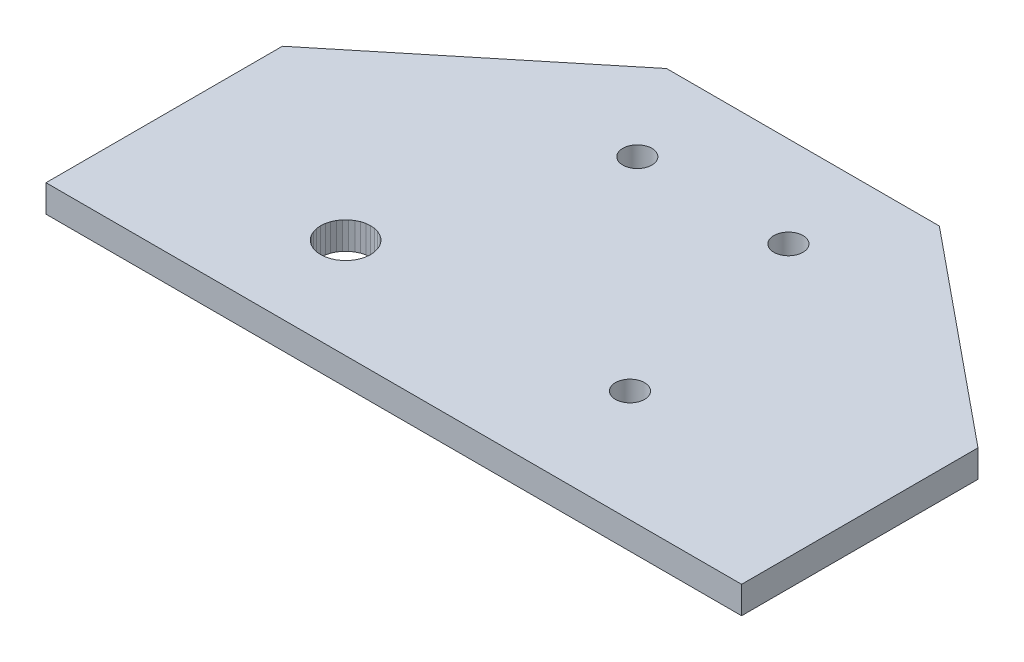
SolidWorks part; units mm, degrees
ref_plane "Front Plane" through (0, 0, 0) normal (0, 0, 1) x (1, 0, 0)
ref_plane "Top Plane" through (0, 0, 0) normal (0, 1, 0) x (1, 0, 0)
ref_plane "Right Plane" through (0, 0, 0) normal (1, 0, 0) x (0, 0, -1)
ref_plane "Plane1" through (0, 13, 0) normal (0, 1, 0) x (1, 0, 0)
sketch "Sketch1" plane through (0, 13, 0) normal (0, 1, 0) x (1, 0, 0)
  line L0 (0, -45) -> (76.5, -45)
  line L1 (76.5, -45) -> (76.5, -19)
  line L2 (76.5, -19) -> (53.25, 0)
  line L3 (53.25, 0) -> (23.25, 0)
  line L4 (23.25, 0) -> (0, -19)
  line L5 (0, -19) -> (0, -45)
extrude "Boss-Extrude1" add sketch "Sketch1" against normal blind 3
sketch "Sketch2" plane through (0, 10, 0) normal (0, -1, 0) x (1, 0, 0)
  line L0 (24.3316, 35.375) -> (24.0566, 35.7677)
  line L1 (24.0566, 35.7677) -> (23.7177, 36.1066)
  line L2 (23.7177, 36.1066) -> (23.325, 36.3816)
  line L3 (23.325, 36.3816) -> (22.8906, 36.5842)
  line L4 (22.8906, 36.5842) -> (22.4275, 36.7082)
  line L5 (22.4275, 36.7082) -> (21.95, 36.75)
  line L6 (21.95, 36.75) -> (21.4725, 36.7082)
  line L7 (21.4725, 36.7082) -> (21.0094, 36.5842)
  line L8 (21.0094, 36.5842) -> (20.575, 36.3816)
  line L9 (20.575, 36.3816) -> (20.1823, 36.1066)
  line L10 (20.1823, 36.1066) -> (19.8434, 35.7677)
  line L11 (19.8434, 35.7677) -> (19.5684, 35.375)
  line L12 (19.5684, 35.375) -> (19.3658, 34.9406)
  line L13 (19.3658, 34.9406) -> (19.2418, 34.4775)
  line L14 (19.2418, 34.4775) -> (19.2, 34)
  line L15 (19.2, 34) -> (19.2418, 33.5225)
  line L16 (19.2418, 33.5225) -> (19.3658, 33.0594)
  line L17 (19.3658, 33.0594) -> (19.5684, 32.625)
  line L18 (19.5684, 32.625) -> (19.8434, 32.2323)
  line L19 (19.8434, 32.2323) -> (20.1823, 31.8934)
  line L20 (20.1823, 31.8934) -> (20.575, 31.6184)
  line L21 (20.575, 31.6184) -> (21.0094, 31.4158)
  line L22 (21.0094, 31.4158) -> (21.4725, 31.2918)
  line L23 (21.4725, 31.2918) -> (21.95, 31.25)
  line L24 (21.95, 31.25) -> (22.4275, 31.2918)
  line L25 (22.4275, 31.2918) -> (22.8906, 31.4158)
  line L26 (22.8906, 31.4158) -> (23.325, 31.6184)
  line L27 (23.325, 31.6184) -> (23.7177, 31.8934)
  line L28 (23.7177, 31.8934) -> (24.0566, 32.2323)
  line L29 (24.0566, 32.2323) -> (24.3316, 32.625)
  line L30 (24.3316, 32.625) -> (24.5342, 33.0594)
  line L31 (24.5342, 33.0594) -> (24.6582, 33.5225)
  line L32 (24.6582, 33.5225) -> (24.7, 34)
  line L33 (24.7, 34) -> (24.6582, 34.4775)
  line L34 (24.6582, 34.4775) -> (24.5342, 34.9406)
  line L35 (24.5342, 34.9406) -> (24.3316, 35.375)
extrude "Cut-Extrude1" cut sketch "Sketch2" against normal through all
sketch "Sketch3" plane through (0, 13, 0) normal (0, 1, 0) x (-1, 0, 0)
  line L0 (-52.7747, 30.3008) -> (-53.1696, 30.4849)
  line L1 (-53.1696, 30.4849) -> (-53.5266, 30.7349)
  line L2 (-53.5266, 30.7349) -> (-53.8347, 31.043)
  line L3 (-53.8347, 31.043) -> (-54.0847, 31.4)
  line L4 (-54.0847, 31.4) -> (-54.2688, 31.795)
  line L5 (-54.2688, 31.795) -> (-54.3816, 32.2159)
  line L6 (-54.3816, 32.2159) -> (-54.4196, 32.65)
  line L7 (-54.4196, 32.65) -> (-54.3816, 33.0841)
  line L8 (-54.3816, 33.0841) -> (-54.2688, 33.5051)
  line L9 (-54.2688, 33.5051) -> (-54.0847, 33.9)
  line L10 (-54.0847, 33.9) -> (-53.8347, 34.257)
  line L11 (-53.8347, 34.257) -> (-53.5266, 34.5651)
  line L12 (-53.5266, 34.5651) -> (-53.1696, 34.8151)
  line L13 (-53.1696, 34.8151) -> (-52.7747, 34.9992)
  line L14 (-52.7747, 34.9992) -> (-52.3537, 35.112)
  line L15 (-52.3537, 35.112) -> (-51.9196, 35.15)
  line L16 (-51.9196, 35.15) -> (-51.4855, 35.112)
  line L17 (-51.4855, 35.112) -> (-51.0646, 34.9992)
  line L18 (-51.0646, 34.9992) -> (-50.6696, 34.8151)
  line L19 (-50.6696, 34.8151) -> (-50.3126, 34.5651)
  line L20 (-50.3126, 34.5651) -> (-50.0045, 34.257)
  line L21 (-50.0045, 34.257) -> (-49.7545, 33.9)
  line L22 (-49.7545, 33.9) -> (-49.5704, 33.5051)
  line L23 (-49.5704, 33.5051) -> (-49.4576, 33.0841)
  line L24 (-49.4576, 33.0841) -> (-49.4196, 32.65)
  line L25 (-49.4196, 32.65) -> (-49.4576, 32.2159)
  line L26 (-49.4576, 32.2159) -> (-49.5704, 31.795)
  line L27 (-49.5704, 31.795) -> (-49.7545, 31.4)
  line L28 (-49.7545, 31.4) -> (-50.0045, 31.043)
  line L29 (-50.0045, 31.043) -> (-50.3126, 30.7349)
  line L30 (-50.3126, 30.7349) -> (-50.6696, 30.4849)
  line L31 (-50.6696, 30.4849) -> (-51.0646, 30.3008)
  line L32 (-51.0646, 30.3008) -> (-51.4855, 30.188)
  line L33 (-51.4855, 30.188) -> (-51.9196, 30.15)
  line L34 (-51.9196, 30.15) -> (-52.3537, 30.188)
  line L35 (-52.3537, 30.188) -> (-52.7747, 30.3008)
sketch "Sketch4" plane through (0, 13, 0) normal (0, 1, 0) x (-1, 0, 0)
  line L0 (-41.95, 10.3473) -> (-41.9196, 10)
  line L1 (-41.9196, 10) -> (-41.95, 9.6527)
  line L2 (-41.95, 9.6527) -> (-42.0402, 9.316)
  line L3 (-42.0402, 9.316) -> (-42.1876, 9)
  line L4 (-42.1876, 9) -> (-42.3875, 8.7144)
  line L5 (-42.3875, 8.7144) -> (-42.634, 8.4679)
  line L6 (-42.634, 8.4679) -> (-42.9196, 8.268)
  line L7 (-42.9196, 8.268) -> (-43.2356, 8.1206)
  line L8 (-43.2356, 8.1206) -> (-43.5723, 8.0304)
  line L9 (-43.5723, 8.0304) -> (-43.9196, 8)
  line L10 (-43.9196, 8) -> (-44.2669, 8.0304)
  line L11 (-44.2669, 8.0304) -> (-44.6036, 8.1206)
  line L12 (-44.6036, 8.1206) -> (-44.9196, 8.268)
  line L13 (-44.9196, 8.268) -> (-45.2052, 8.4679)
  line L14 (-45.2052, 8.4679) -> (-45.4517, 8.7144)
  line L15 (-45.4517, 8.7144) -> (-45.6517, 9)
  line L16 (-45.6517, 9) -> (-45.799, 9.316)
  line L17 (-45.799, 9.316) -> (-45.8892, 9.6527)
  line L18 (-45.8892, 9.6527) -> (-45.9196, 10)
  line L19 (-45.9196, 10) -> (-45.8892, 10.3473)
  line L20 (-45.8892, 10.3473) -> (-45.799, 10.684)
  line L21 (-45.799, 10.684) -> (-45.6517, 11)
  line L22 (-45.6517, 11) -> (-45.4517, 11.2856)
  line L23 (-45.4517, 11.2856) -> (-45.2052, 11.5321)
  line L24 (-45.2052, 11.5321) -> (-44.9196, 11.7321)
  line L25 (-44.9196, 11.7321) -> (-44.6036, 11.8794)
  line L26 (-44.6036, 11.8794) -> (-44.2669, 11.9696)
  line L27 (-44.2669, 11.9696) -> (-43.9196, 12)
  line L28 (-43.9196, 12) -> (-43.5723, 11.9696)
  line L29 (-43.5723, 11.9696) -> (-43.2356, 11.8794)
  line L30 (-43.2356, 11.8794) -> (-42.9196, 11.7321)
  line L31 (-42.9196, 11.7321) -> (-42.634, 11.5321)
  line L32 (-42.634, 11.5321) -> (-42.3875, 11.2856)
  line L33 (-42.3875, 11.2856) -> (-42.1876, 11)
  line L34 (-42.1876, 11) -> (-42.0402, 10.684)
  line L35 (-42.0402, 10.684) -> (-41.95, 10.3473)
extrude "Boss-Extrude3" add sketch "Sketch4" along normal blind 5
sketch "Sketch5" plane through (0, 13, 0) normal (0, 1, 0) x (-1, 0, 0)
  line L0 (-30.95, 11.7321) -> (-30.634, 11.8794)
  line L1 (-30.634, 11.8794) -> (-30.2973, 11.9696)
  line L2 (-30.2973, 11.9696) -> (-29.95, 12)
  line L3 (-29.95, 12) -> (-29.6027, 11.9696)
  line L4 (-29.6027, 11.9696) -> (-29.266, 11.8794)
  line L5 (-29.266, 11.8794) -> (-28.95, 11.7321)
  line L6 (-28.95, 11.7321) -> (-28.6644, 11.5321)
  line L7 (-28.6644, 11.5321) -> (-28.4179, 11.2856)
  line L8 (-28.4179, 11.2856) -> (-28.2179, 11)
  line L9 (-28.2179, 11) -> (-28.0706, 10.684)
  line L10 (-28.0706, 10.684) -> (-27.9804, 10.3473)
  line L11 (-27.9804, 10.3473) -> (-27.95, 10)
  line L12 (-27.95, 10) -> (-27.9804, 9.6527)
  line L13 (-27.9804, 9.6527) -> (-28.0706, 9.316)
  line L14 (-28.0706, 9.316) -> (-28.2179, 9)
  line L15 (-28.2179, 9) -> (-28.4179, 8.7144)
  line L16 (-28.4179, 8.7144) -> (-28.6644, 8.4679)
  line L17 (-28.6644, 8.4679) -> (-28.95, 8.268)
  line L18 (-28.95, 8.268) -> (-29.266, 8.1206)
  line L19 (-29.266, 8.1206) -> (-29.6027, 8.0304)
  line L20 (-29.6027, 8.0304) -> (-29.95, 8)
  line L21 (-29.95, 8) -> (-30.2973, 8.0304)
  line L22 (-30.2973, 8.0304) -> (-30.634, 8.1206)
  line L23 (-30.634, 8.1206) -> (-30.95, 8.268)
  line L24 (-30.95, 8.268) -> (-31.2356, 8.4679)
  line L25 (-31.2356, 8.4679) -> (-31.4821, 8.7144)
  line L26 (-31.4821, 8.7144) -> (-31.6821, 9)
  line L27 (-31.6821, 9) -> (-31.8294, 9.316)
  line L28 (-31.8294, 9.316) -> (-31.9196, 9.6527)
  line L29 (-31.9196, 9.6527) -> (-31.95, 10)
  line L30 (-31.95, 10) -> (-31.9196, 10.3473)
  line L31 (-31.9196, 10.3473) -> (-31.8294, 10.684)
  line L32 (-31.8294, 10.684) -> (-31.6821, 11)
  line L33 (-31.6821, 11) -> (-31.4821, 11.2856)
  line L34 (-31.4821, 11.2856) -> (-31.2356, 11.5321)
  line L35 (-31.2356, 11.5321) -> (-30.95, 11.7321)
sketch "Sketch6" plane through (0, 10, 0) normal (0, -1, 0) x (1, 0, 0)
  line L0 (54.25, 33.9689) -> (53.7502, 34.3188)
  line L1 (53.7502, 34.3188) -> (53.3188, 34.7502)
  line L2 (53.3188, 34.7502) -> (52.9689, 35.25)
  line L3 (52.9689, 35.25) -> (52.7111, 35.8029)
  line L4 (52.7111, 35.8029) -> (52.5532, 36.3922)
  line L5 (52.5532, 36.3922) -> (52.5, 37)
  line L6 (52.5, 37) -> (52.5532, 37.6078)
  line L7 (52.5532, 37.6078) -> (52.7111, 38.1971)
  line L8 (52.7111, 38.1971) -> (52.9689, 38.75)
  line L9 (52.9689, 38.75) -> (53.3188, 39.2498)
  line L10 (53.3188, 39.2498) -> (53.7502, 39.6812)
  line L11 (53.7502, 39.6812) -> (54.25, 40.0311)
  line L12 (54.25, 40.0311) -> (54.8029, 40.2889)
  line L13 (54.8029, 40.2889) -> (55.3922, 40.4468)
  line L14 (55.3922, 40.4468) -> (56, 40.5)
  line L15 (56, 40.5) -> (56.6078, 40.4468)
  line L16 (56.6078, 40.4468) -> (57.1971, 40.2889)
  line L17 (57.1971, 40.2889) -> (57.75, 40.0311)
  line L18 (57.75, 40.0311) -> (58.2498, 39.6812)
  line L19 (58.2498, 39.6812) -> (58.6812, 39.2498)
  line L20 (58.6812, 39.2498) -> (59.0311, 38.75)
  line L21 (59.0311, 38.75) -> (59.2889, 38.1971)
  line L22 (59.2889, 38.1971) -> (59.4468, 37.6078)
  line L23 (59.4468, 37.6078) -> (59.5, 37)
  line L24 (59.5, 37) -> (59.4468, 36.3922)
  line L25 (59.4468, 36.3922) -> (59.2889, 35.8029)
  line L26 (59.2889, 35.8029) -> (59.0311, 35.25)
  line L27 (59.0311, 35.25) -> (58.6812, 34.7502)
  line L28 (58.6812, 34.7502) -> (58.2498, 34.3188)
  line L29 (58.2498, 34.3188) -> (57.75, 33.9689)
  line L30 (57.75, 33.9689) -> (57.1971, 33.7111)
  line L31 (57.1971, 33.7111) -> (56.6078, 33.5532)
  line L32 (56.6078, 33.5532) -> (56, 33.5)
  line L33 (56, 33.5) -> (55.3922, 33.5532)
  line L34 (55.3922, 33.5532) -> (54.8029, 33.7111)
  line L35 (54.8029, 33.7111) -> (54.25, 33.9689)
sketch "Sketch8" plane through (0, 10, 0) normal (0, -1, 0) x (1, 0, 0)
  line L0 (54.8029, 23.7111) -> (54.25, 23.9689)
  line L1 (54.25, 23.9689) -> (53.7502, 24.3188)
  line L2 (53.7502, 24.3188) -> (53.3188, 24.7502)
  line L3 (53.3188, 24.7502) -> (52.9689, 25.25)
  line L4 (52.9689, 25.25) -> (52.7111, 25.8029)
  line L5 (52.7111, 25.8029) -> (52.5532, 26.3922)
  line L6 (52.5532, 26.3922) -> (52.5, 27)
  line L7 (52.5, 27) -> (52.5532, 27.6078)
  line L8 (52.5532, 27.6078) -> (52.7111, 28.1971)
  line L9 (52.7111, 28.1971) -> (52.9689, 28.75)
  line L10 (52.9689, 28.75) -> (53.3188, 29.2498)
  line L11 (53.3188, 29.2498) -> (53.7502, 29.6812)
  line L12 (53.7502, 29.6812) -> (54.25, 30.0311)
  line L13 (54.25, 30.0311) -> (54.8029, 30.2889)
  line L14 (54.8029, 30.2889) -> (55.3922, 30.4468)
  line L15 (55.3922, 30.4468) -> (56, 30.5)
  line L16 (56, 30.5) -> (56.6078, 30.4468)
  line L17 (56.6078, 30.4468) -> (57.1971, 30.2889)
  line L18 (57.1971, 30.2889) -> (57.75, 30.0311)
  line L19 (57.75, 30.0311) -> (58.2498, 29.6812)
  line L20 (58.2498, 29.6812) -> (58.6812, 29.2498)
  line L21 (58.6812, 29.2498) -> (59.0311, 28.75)
  line L22 (59.0311, 28.75) -> (59.2889, 28.1971)
  line L23 (59.2889, 28.1971) -> (59.4468, 27.6078)
  line L24 (59.4468, 27.6078) -> (59.5, 27)
  line L25 (59.5, 27) -> (59.4468, 26.3922)
  line L26 (59.4468, 26.3922) -> (59.2889, 25.8029)
  line L27 (59.2889, 25.8029) -> (59.0311, 25.25)
  line L28 (59.0311, 25.25) -> (58.6812, 24.7502)
  line L29 (58.6812, 24.7502) -> (58.2498, 24.3188)
  line L30 (58.2498, 24.3188) -> (57.75, 23.9689)
  line L31 (57.75, 23.9689) -> (57.1971, 23.7111)
  line L32 (57.1971, 23.7111) -> (56.6078, 23.5532)
  line L33 (56.6078, 23.5532) -> (56, 23.5)
  line L34 (56, 23.5) -> (55.3922, 23.5532)
  line L35 (55.3922, 23.5532) -> (54.8029, 23.7111)
sketch "Sketch10" plane through (0, 10, 0) normal (0, -1, 0) x (1, 0, 0)
  line L0 (4.5532, 36.3922) -> (4.5, 37)
  line L1 (4.5, 37) -> (4.5532, 37.6078)
  line L2 (4.5532, 37.6078) -> (4.7111, 38.1971)
  line L3 (4.7111, 38.1971) -> (4.9689, 38.75)
  line L4 (4.9689, 38.75) -> (5.3188, 39.2498)
  line L5 (5.3188, 39.2498) -> (5.7502, 39.6812)
  line L6 (5.7502, 39.6812) -> (6.25, 40.0311)
  line L7 (6.25, 40.0311) -> (6.8029, 40.2889)
  line L8 (6.8029, 40.2889) -> (7.3922, 40.4468)
  line L9 (7.3922, 40.4468) -> (8, 40.5)
  line L10 (8, 40.5) -> (8.6078, 40.4468)
  line L11 (8.6078, 40.4468) -> (9.1971, 40.2889)
  line L12 (9.1971, 40.2889) -> (9.75, 40.0311)
  line L13 (9.75, 40.0311) -> (10.2498, 39.6812)
  line L14 (10.2498, 39.6812) -> (10.6812, 39.2498)
  line L15 (10.6812, 39.2498) -> (11.0311, 38.75)
  line L16 (11.0311, 38.75) -> (11.2889, 38.1971)
  line L17 (11.2889, 38.1971) -> (11.4468, 37.6078)
  line L18 (11.4468, 37.6078) -> (11.5, 37)
  line L19 (11.5, 37) -> (11.4468, 36.3922)
  line L20 (11.4468, 36.3922) -> (11.2889, 35.8029)
  line L21 (11.2889, 35.8029) -> (11.0311, 35.25)
  line L22 (11.0311, 35.25) -> (10.6812, 34.7502)
  line L23 (10.6812, 34.7502) -> (10.2498, 34.3188)
  line L24 (10.2498, 34.3188) -> (9.75, 33.9689)
  line L25 (9.75, 33.9689) -> (9.1971, 33.7111)
  line L26 (9.1971, 33.7111) -> (8.6078, 33.5532)
  line L27 (8.6078, 33.5532) -> (8, 33.5)
  line L28 (8, 33.5) -> (7.3922, 33.5532)
  line L29 (7.3922, 33.5532) -> (6.8029, 33.7111)
  line L30 (6.8029, 33.7111) -> (6.25, 33.9689)
  line L31 (6.25, 33.9689) -> (5.7502, 34.3188)
  line L32 (5.7502, 34.3188) -> (5.3188, 34.7502)
  line L33 (5.3188, 34.7502) -> (4.9689, 35.25)
  line L34 (4.9689, 35.25) -> (4.7111, 35.8029)
  line L35 (4.7111, 35.8029) -> (4.5532, 36.3922)
sketch "Sketch12" plane through (0, 10, 0) normal (0, -1, 0) x (1, 0, 0)
  line L0 (7.3922, 23.5532) -> (6.8029, 23.7111)
  line L1 (6.8029, 23.7111) -> (6.25, 23.9689)
  line L2 (6.25, 23.9689) -> (5.7502, 24.3188)
  line L3 (5.7502, 24.3188) -> (5.3188, 24.7502)
  line L4 (5.3188, 24.7502) -> (4.9689, 25.25)
  line L5 (4.9689, 25.25) -> (4.7111, 25.8029)
  line L6 (4.7111, 25.8029) -> (4.5532, 26.3922)
  line L7 (4.5532, 26.3922) -> (4.5, 27)
  line L8 (4.5, 27) -> (4.5532, 27.6078)
  line L9 (4.5532, 27.6078) -> (4.7111, 28.1971)
  line L10 (4.7111, 28.1971) -> (4.9689, 28.75)
  line L11 (4.9689, 28.75) -> (5.3188, 29.2498)
  line L12 (5.3188, 29.2498) -> (5.7502, 29.6812)
  line L13 (5.7502, 29.6812) -> (6.25, 30.0311)
  line L14 (6.25, 30.0311) -> (6.8029, 30.2889)
  line L15 (6.8029, 30.2889) -> (7.3922, 30.4468)
  line L16 (7.3922, 30.4468) -> (8, 30.5)
  line L17 (8, 30.5) -> (8.6078, 30.4468)
  line L18 (8.6078, 30.4468) -> (9.1971, 30.2889)
  line L19 (9.1971, 30.2889) -> (9.75, 30.0311)
  line L20 (9.75, 30.0311) -> (10.2498, 29.6812)
  line L21 (10.2498, 29.6812) -> (10.6812, 29.2498)
  line L22 (10.6812, 29.2498) -> (11.0311, 28.75)
  line L23 (11.0311, 28.75) -> (11.2889, 28.1971)
  line L24 (11.2889, 28.1971) -> (11.4468, 27.6078)
  line L25 (11.4468, 27.6078) -> (11.5, 27)
  line L26 (11.5, 27) -> (11.4468, 26.3922)
  line L27 (11.4468, 26.3922) -> (11.2889, 25.8029)
  line L28 (11.2889, 25.8029) -> (11.0311, 25.25)
  line L29 (11.0311, 25.25) -> (10.6812, 24.7502)
  line L30 (10.6812, 24.7502) -> (10.2498, 24.3188)
  line L31 (10.2498, 24.3188) -> (9.75, 23.9689)
  line L32 (9.75, 23.9689) -> (9.1971, 23.7111)
  line L33 (9.1971, 23.7111) -> (8.6078, 23.5532)
  line L34 (8.6078, 23.5532) -> (8, 23.5)
  line L35 (8, 23.5) -> (7.3922, 23.5532)
sketch "Sketch14" plane through (0, 13, 0) normal (0, 1, 0) x (1, 0, 0)
  circle A0 centre (43.9728, -10.1395) radius 2.5833
extrude "Cut-Extrude6" cut sketch "Sketch14" along normal blind 8
hole_wizard "M3 Clearance Hole2" positions "Sketch17" profile "Sketch18" hole size "M3" standard "ANSI Metric" end condition through all
sketch "Sketch17" plane through (0, 13, 0) normal (0, 1, 0) x (1, 0, 0)
  point P0 (30.0404, -10.0063)
  point P2 (46.6565, -10.0063)
sketch "Sketch18" plane through (30.0404, 13, 10.0063) normal (1, 0, 0) x (0, 0, 1)
  line L0 (0, 0) -> (0, 3)
  line L1 (0, 3) -> (1.6, 3)
  line L2 (1.6, 3) -> (1.6, 0)
  line L5 (1.6, 0) -> (0, 0)
  line L11 (0, -6.35) -> (0, 107.95) construction
  dimension "Thru Hole Dia." = 3.2
  dimension "Thru Hole Depth" = 3
hole_wizard "M3 Clearance Hole3" positions "Sketch19" profile "Sketch20" hole size "M3" standard "ANSI Metric" end condition through all
sketch "Sketch19" plane through (0, 13, 0) normal (0, 1, 0) x (1, 0, 0)
  point P0 (51.9535, -32.7277)
sketch "Sketch20" plane through (51.9535, 13, 32.7277) normal (1, 0, 0) x (0, 0, 1)
  line L0 (0, 0) -> (0, 3)
  line L1 (0, 3) -> (1.6, 3)
  line L2 (1.6, 3) -> (1.6, 0)
  line L5 (1.6, 0) -> (0, 0)
  line L11 (0, -6.35) -> (0, 107.95) construction
  dimension "Thru Hole Dia." = 3.2
  dimension "Thru Hole Depth" = 3
